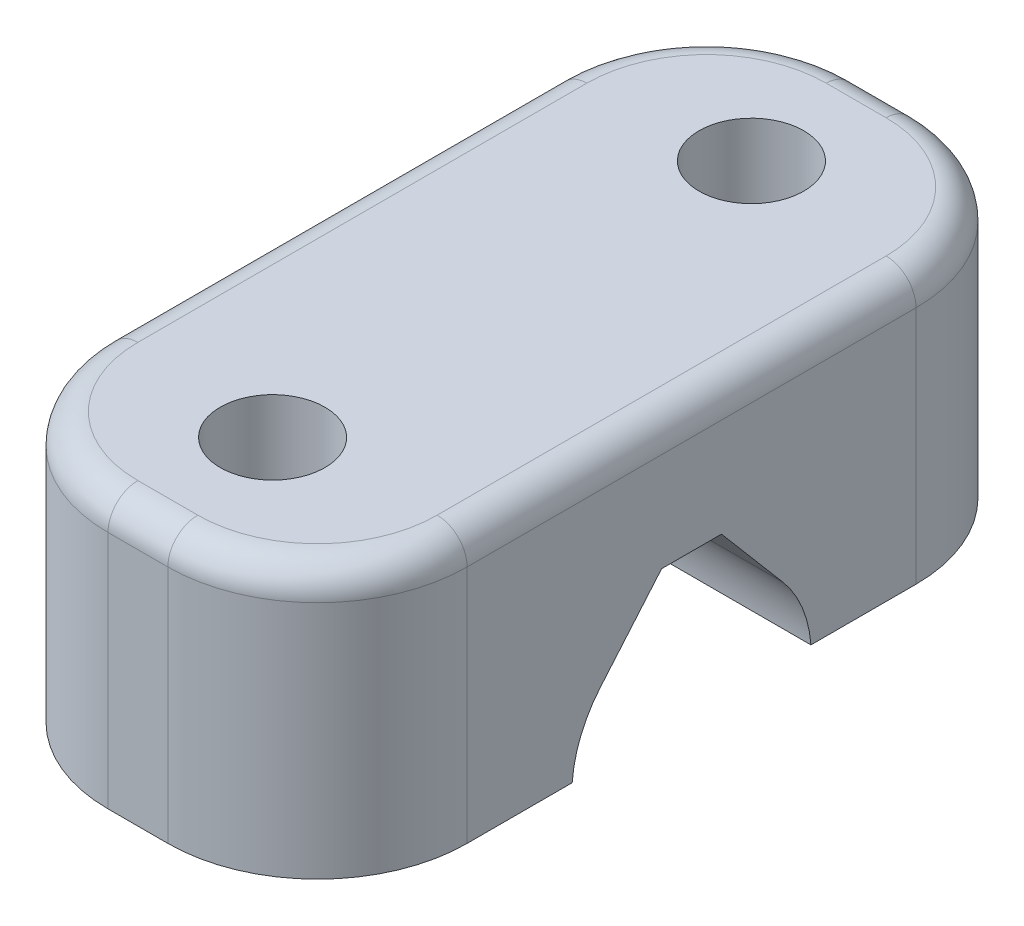
SolidWorks part; units mm, degrees
ref_plane "Alzado" through (0, 0, 0) normal (0, 0, 1) x (1, 0, 0)
ref_plane "Planta" through (0, 0, 0) normal (0, 1, 0) x (1, 0, 0)
ref_plane "Vista lateral" through (0, 0, 0) normal (1, 0, 0) x (0, 0, -1)
sketch "Croquis1" plane through (0, 0, 0) normal (0, 1, 0) x (1, 0, 0)
  line L0 (0, -55) -> (0, 55) construction
  line L1 (0, 12.5) -> (12, 12.5)
  line L2 (0, 12.5) -> (0, -12.5)
  line L3 (0, -12.5) -> (12, -12.5)
  line L4 (12, 12.5) -> (12, -12.5)
  line L5 (-8.7591, 0) -> (38.4995, 0) construction
  line L6 (-55, 0) -> (55, 0) construction
  dimension "D1" = 25
  dimension "D2" = 12
extrude "Saliente-Extruir1" add sketch "Croquis1" along normal blind 9
sketch "Croquis3" plane through (0, 0, 0) normal (1, 0, 0) x (0, 0, -1)
  line L0 (-3.0479, 2.2904) -> (-1, 4.7)
  line L1 (-1, 4.7) -> (1, 4.7)
  line L2 (1, 4.7) -> (3.0479, 2.2904)
  line L3 (0, 9.5392) -> (0, -5.3638) construction
  line L4 (0, 4.95) -> (0, -4.95) construction
  line L5 (6.6, 0) -> (-6.6, 0) construction
  arc A0 (-3.0479, 2.2904) -> (3.0479, 2.2904) centre (0, -0.3) ccw
  dimension "D1" = 8
  dimension "D2" = 2
  dimension "D3" = 5
  dimension "D4" = 0.3
extrude "Cortar-Extruir1" cut sketch "Croquis3" along normal through all
sketch "Croquis4" plane through (0, 0, 0) normal (0, -1, 0) x (1, 0, 0)
  line L0 (-0.9259, 0) -> (32.8144, 0) construction
  line L1 (4.95, 0) -> (-4.95, 0) construction
  line L2 (12, 12.5) -> (12, 3.9887) construction
  circle A0 centre (6, 8) radius 1.75
  circle A3 centre (6, -8) radius 1.75
  dimension "D3" = 3.5
  dimension "D1" = 16
  dimension "D2" = 6
extrude "Cortar-Extruir2" cut sketch "Croquis4" against normal through all
fillet "Redondeo1" radius 5 4 edges at (0, 4.5, -12.5) (12, 4.5, -12.5) (12, 4.5, 12.5) (0, 4.5, 12.5)
fillet "Redondeo2" radius 1 8 edges at (10.5355, 9, -11.0355) (12, 9, 0) (10.5355, 9, 11.0355) (6, 9, 12.5) (1.4645, 9, 11.0355) (0, 9, 0) (1.4645, 9, -11.0355) (6, 9, -12.5)
